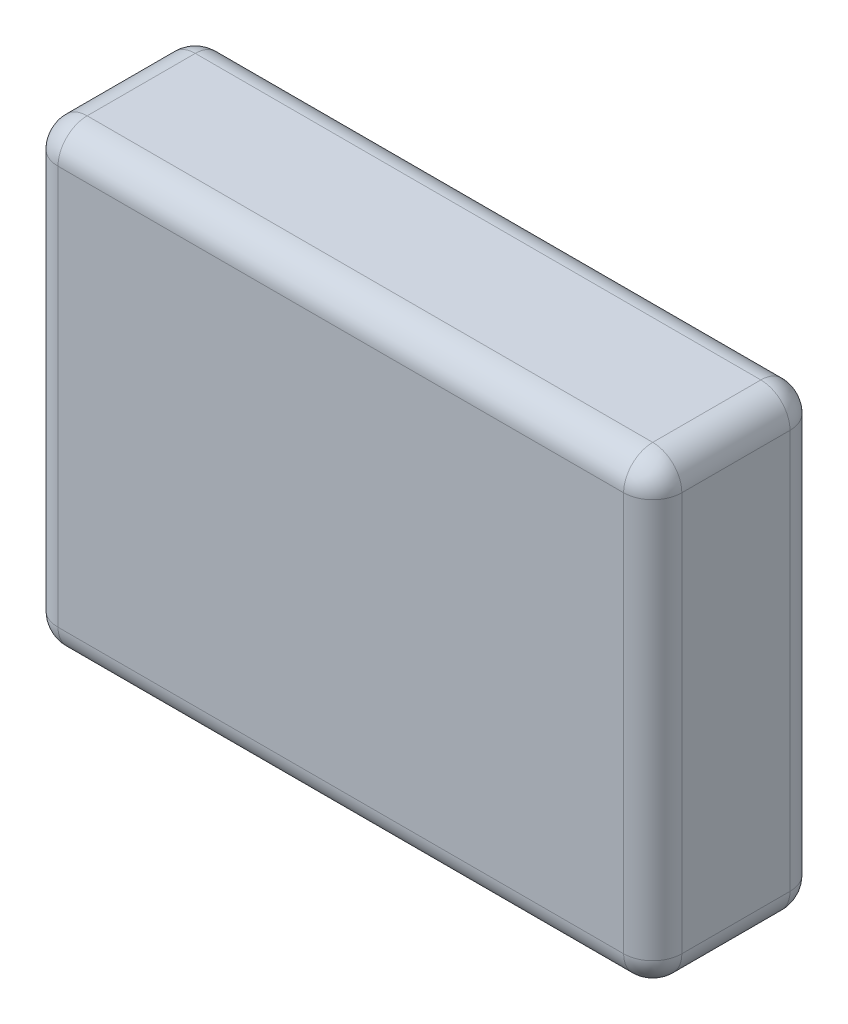
SolidWorks part; units mm, degrees
ref_plane "Front Plane" through (0, 0, 0) normal (0, 0, 1) x (1, 0, 0)
ref_plane "Top Plane" through (0, 0, 0) normal (0, 1, 0) x (1, 0, 0)
ref_plane "Right Plane" through (0, 0, 0) normal (1, 0, 0) x (0, 0, -1)
sketch "Sketch1" plane through (0, 0, 0) normal (0, 0, 1) x (1, 0, 0)
  line L1 (-375, 172.2716) -> (375, 172.2716)
  line L2 (-375, 172.2716) -> (-375, -377.7284)
  line L3 (-375, -377.7284) -> (375, -377.7284)
  line L4 (375, 172.2716) -> (375, -377.7284)
  line L5 (-375, 172.2716) -> (375, -377.7284) construction
  line L6 (-375, -377.7284) -> (375, 172.2716) construction
  point P0 (0, 0)
  point P5 (-375, -377.7284)
  dimension "D1" = 750
  dimension "D2" = 550
extrude "Boss-Extrude1" add sketch "Sketch1" along normal blind 200
fillet "Fillet3" radius 35 12 edges at (375, 172.2716, 100) (-375, 172.2716, 100) (-375, -377.7284, 100) (375, -377.7284, 100) (0, -377.7284, 200) (-375, -102.7284, 200) (0, 172.2716, 200) (375, -102.7284, 200) (0, -377.7284, 0) (-375, -102.7284, 0) (0, 172.2716, 0) (375, -102.7284, 0)
